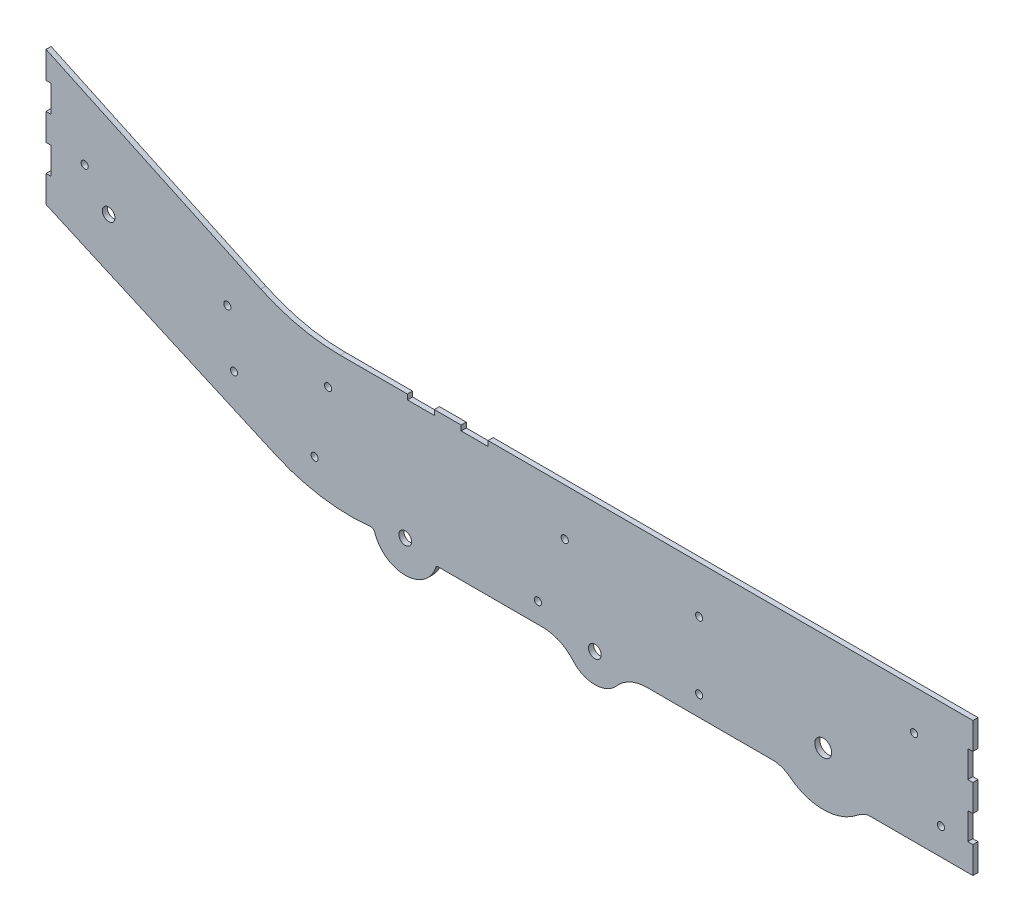
SolidWorks part; units mm, degrees
ref_plane "Front Plane" through (0, 0, 0) normal (0, 0, 1) x (1, 0, 0)
ref_plane "Top Plane" through (0, 0, 0) normal (0, 1, 0) x (1, 0, 0)
ref_plane "Right Plane" through (0, 0, 0) normal (1, 0, 0) x (0, 0, -1)
ref_plane "Plane1" through (0, 0, 0) normal (0, 0, -1) x (-1, 0, 0)
sketch "Sketch1" plane through (0, 0, 0) normal (0, 0, -1) x (-1, 0, 0)
  line L0 (534.6067, 122.174) -> (509.2067, 122.174)
  line L1 (509.2067, 122.174) -> (509.2067, 127)
  line L2 (509.2067, 127) -> (483.8067, 127)
  line L3 (483.8067, 127) -> (483.8067, 122.174)
  line L4 (483.8067, 122.174) -> (458.4067, 122.174)
  line L5 (458.4067, 122.174) -> (458.4067, 127)
  line L6 (458.4067, 127) -> (0, 127)
  line L7 (0, 127) -> (0, 101.6)
  line L8 (0, 101.6) -> (4.826, 101.6)
  line L9 (4.826, 101.6) -> (4.826, 76.2)
  line L10 (4.826, 76.2) -> (0, 76.2)
  line L11 (0, 76.2) -> (0, 50.8)
  line L12 (0, 50.8) -> (4.826, 50.8)
  line L13 (4.826, 50.8) -> (4.826, 25.4)
  line L14 (4.826, 25.4) -> (0, 25.4)
  line L15 (0, 0) -> (0, 25.4)
  line L16 (0, 0) -> (98.9962, 0)
  line L17 (189.6182, 0) -> (308.1168, 0)
  line L18 (406.6463, 0) -> (506.2014, 0)
  line L19 (659.7562, 15.1211) -> (876.3, 111.3431)
  line L20 (876.3, 111.3431) -> (876.3, 136.7431)
  line L21 (876.3, 136.7431) -> (871.474, 136.7431)
  line L22 (871.474, 136.7431) -> (871.474, 162.1431)
  line L23 (871.474, 162.1431) -> (876.3, 162.1431)
  line L24 (876.3, 162.1431) -> (876.3, 187.5431)
  line L25 (876.3, 187.5431) -> (871.474, 187.5431)
  line L26 (871.474, 187.5431) -> (871.474, 212.9431)
  line L27 (871.474, 212.9431) -> (876.3, 212.9431)
  line L28 (876.3, 212.9431) -> (876.3, 238.3431)
  line L29 (876.3, 238.3431) -> (673.2483, 143.6585)
  line L30 (598.1067, 127) -> (534.6067, 127)
  line L31 (534.6067, 127) -> (534.6067, 122.174)
  line L32 (324.0408, -32.4456) -> (382.7479, -32.4456) construction
  circle A0 centre (698.5, 63.5) radius 3.3782
  circle A1 centre (704.85, 114.3) radius 3.3782
  circle A2 centre (30.226, 25.4) radius 3.3782
  circle A3 centre (622.3, 31.75) radius 3.3782
  circle A4 centre (411.2514, 19.05) radius 3.3782
  circle A5 centre (385.8514, 82.55) radius 3.3782
  circle A6 centre (258.8514, 82.55) radius 3.3782
  circle A7 centre (258.8514, 19.05) radius 3.3782
  circle A8 centre (55.626, 88.9) radius 3.3782
  circle A9 centre (609.6, 95.25) radius 3.3782
  circle A10 centre (839.724, 162.1431) radius 3.3782
  circle A11 centre (141.5067, 33.811) radius 8
  circle A12 centre (357.4067, 4.8294) radius 6
  circle A13 centre (536.6967, 8.0094) radius 6
  circle A14 centre (817.1067, 132.8694) radius 6
  arc A15 (98.9962, 0) -> (109.5628, -5.3406) centre (92.1321, -26.7044) cw
  arc A16 (109.5628, -5.3406) -> (172.8412, -5.83) centre (141.5067, 33.811) ccw
  arc A17 (172.8412, -5.83) -> (189.6182, 0) centre (189.6182, -27.0545) cw
  arc A18 (308.1168, 0) -> (336.8475, -13.0768) centre (308.1168, -38.1) cw
  arc A19 (336.8475, -13.0768) -> (377.9798, -13.061) centre (357.4067, 4.8294) ccw
  arc A20 (377.9798, -13.061) -> (406.6463, 0) centre (406.6463, -37.9894) cw
  arc A21 (506.2014, 0) -> (507.5608, -1.0025) centre (506.2014, -1.423) cw
  arc A22 (507.5608, -1.0025) -> (565.6092, -1.6953) centre (536.6967, 8.0094) ccw
  arc A23 (565.6092, -1.6953) -> (569.8082, 0.997) centre (569.3844, -2.9625) cw
  arc A24 (569.8082, 0.997) -> (659.7562, 15.1211) centre (588.489, 175.5052) ccw
  arc A25 (673.2483, 143.6585) -> (598.1067, 127) centre (598.1067, 304.8) cw
  circle A26 centre (357.4067, 4.8294) radius 37.275 construction
  dimension "D12" = 3.18
  dimension "D13" = 74.55
  dimension "D1" = 876.3
  dimension "D2" = 4.826
  dimension "D3" = 127
  dimension "D4" = 76.2
  dimension "D5" = 63.5
  dimension "D6" = 4.826
  dimension "D7" = 215.9
  dimension "D8" = 28.9817
  dimension "D9" = 459.7
  dimension "D10" = 128.04
  dimension "D11" = 179.29
  dimension "D14" = 32.4456
other "AlignGroup1"
other "AlignGroup2"
extrude "Boss-Extrude1" add sketch "Sketch1" against normal blind 4.826
